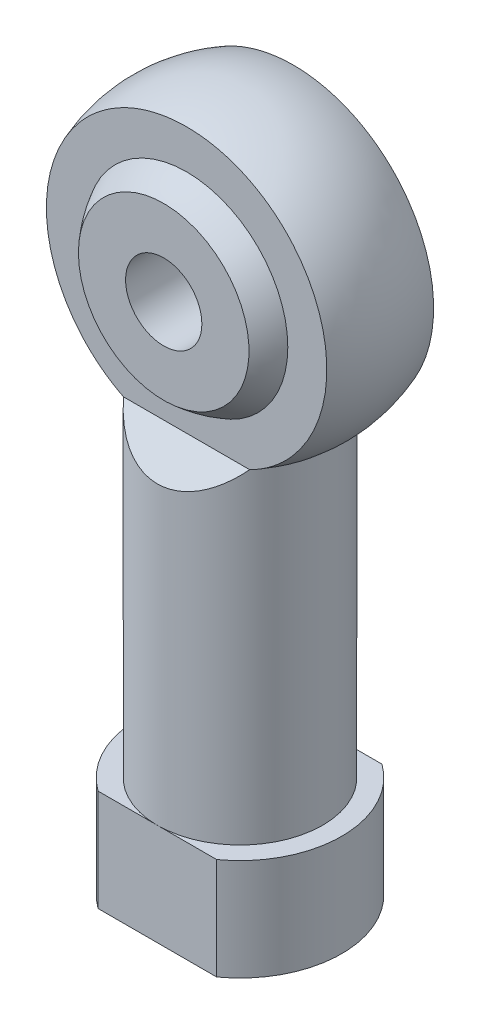
SolidWorks part; units mm, degrees
ref_plane "Alzado" through (0, 0, 0) normal (0, 0, 1) x (1, 0, 0)
ref_plane "Planta" through (0, 0, 0) normal (0, 1, 0) x (1, 0, 0)
ref_plane "Vista lateral" through (0, 0, 0) normal (1, 0, 0) x (0, 0, -1)
sketch "Croquis1" plane through (0, 0, 0) normal (0, 0, 1) x (1, 0, 0)
  line L0 (0, 0) -> (0, 17.2)
  line L1 (0, 0) -> (4, 0)
  line L2 (4, 0) -> (4, 4)
  line L3 (4, 4) -> (3.25, 4)
  line L4 (3.25, 4) -> (3.25, 16.7758)
  line L5 (0, 26.2) -> (0, 27.6)
  arc A0 (3.25, 16.7758) -> (0, 27.6) centre (0, 21.7) ccw
  arc A1 (0, 17.2) -> (0, 26.2) centre (0, 21.7) ccw
  dimension "D2" = 11.8
  dimension "D6" = 9
  dimension "D1" = 27.6
  dimension "D3" = 3.25
  dimension "D4" = 4
  dimension "D5" = 4
revolve "Revolución1" add sketch "Croquis1" angle 360 about L0
sketch "Croquis2" plane through (0, 0, 0) normal (1, 0, 0) x (0, 0, -1)
  line L0 (-3.25, 4) -> (-3.25, 0)
  line L5 (4, 4) -> (-4, 4) construction
  line L6 (-3.25, 16.7758) -> (-3.25, 4) construction
  line L7 (-4, 0) -> (4, 0) construction
  line L8 (-3.25, 4) -> (-4, 4)
  line L9 (-4, 4) -> (-4, 0)
  line L10 (-4, 0) -> (-3.25, 0)
  line L11 (0, -1000) -> (0, 49000) construction
  line L12 (3.25, 16.7758) -> (-3.25, 16.7758) construction
  line L13 (-2.1, 16.7758) -> (-5.9, 16.7758)
  line L14 (-2.1, 16.7758) -> (-2.1, 27.6)
  line L15 (-2.1, 27.6) -> (-5.9, 27.6)
  line L16 (-5.9, 16.7758) -> (-5.9, 27.6)
  line L17 (4, 0) -> (3.25, 0)
  line L18 (4, 4) -> (4, 0)
  line L19 (3.25, 4) -> (4, 4)
  line L20 (3.25, 4) -> (3.25, 0)
  line L21 (2.1, 27.6) -> (5.9, 27.6)
  line L22 (5.9, 16.7758) -> (5.9, 27.6)
  line L23 (2.1, 16.7758) -> (5.9, 16.7758)
  line L24 (2.1, 16.7758) -> (2.1, 27.6)
  line L25 (-2.1, 16.7758) -> (-3.25, 15.6258)
  line L26 (-3.25, 15.6258) -> (-3.25, 16.7758)
  line L27 (-3.25, 16.7758) -> (-3.25, 4) construction
  line L29 (2.1, 16.7758) -> (3.25, 15.6258)
  line L30 (3.25, 15.6258) -> (3.25, 16.7758)
  arc A0 (3.25, 16.7758) -> (-3.25, 16.7758) centre (0, 21.7) ccw construction
  dimension "D1" = 4.2
  dimension "D2" = 45
extrude "Cortar-Extruir1" cut sketch "Croquis2" against normal through all both and the other way through all contours L16 L13 L14 L15 | L24 L23 L22 L21 | L26 L25 L13 | L29 L30 L23 | L19 L20 L17 L18 | L9 L10 L0 L8
sketch "Croquis3" plane through (0, 0, 0) normal (0, 0, 1) x (1, 0, 0)
  line L0 (0, 26.2) -> (0, 17.2)
  arc A0 (0, 26.2) -> (0, 17.2) centre (0, 21.7) ccw
  circle A1 centre (0, 21.7) radius 4.5 construction
  dimension "D1" = 9
revolve "Revolución2" add sketch "Croquis3" angle 360 about L0
sketch "Croquis4" plane through (0, 0, 0) normal (1, 0, 0) x (0, 0, -1)
  line L0 (0, -1000) -> (0, 49000) construction
  line L1 (-3, 18.3459) -> (-4.8775, 18.3459)
  line L2 (-3, 18.3459) -> (-3, 25.0892)
  line L3 (-3, 25.0892) -> (-4.8775, 25.0892)
  line L4 (-4.8775, 18.3459) -> (-4.8775, 25.0892)
  line L5 (3, 25.0892) -> (4.8775, 25.0892)
  line L6 (4.8775, 18.3459) -> (4.8775, 25.0892)
  line L7 (3, 18.3459) -> (4.8775, 18.3459)
  line L8 (3, 18.3459) -> (3, 25.0892)
  arc A0 (-2.1, 25.6799) -> (-2.1, 17.7201) centre (0, 21.7) ccw construction
  dimension "D1" = 6
extrude "Cortar-Extruir2" cut sketch "Croquis4" against normal through all both and the other way through all
sketch "Croquis5" plane through (0, 0, 0) normal (0, 0, 1) x (1, 0, 0)
  circle A0 centre (0, 21.7) radius 1.5
  circle A1 centre (0, 21.7) radius 3.3541 construction
  dimension "D1" = 3
extrude "Cortar-Extruir3" cut sketch "Croquis5" against normal through all both and the other way through all
hole_wizard "Taladro roscado M31" positions "Croquis6" profile "Croquis7" tap size "M3" standard "ISO"
sketch "Croquis6" plane through (0, 0, 0) normal (0, -1, 0) x (-1, 0, 0)
  point P0 (0, 0)
sketch "Croquis7" plane through (0, 0, 0) normal (1, 0, 0) x (0, 0, -1)
  line L0 (0, 0) -> (0, 14.7511)
  line L1 (0, 14.7511) -> (1.25, 14)
  line L2 (1.25, 14) -> (1.25, 0)
  line L5 (1.25, 0) -> (0, 0)
  line L10 (0, 14.7511) -> (-1.25, 14) construction
  line L11 (0, -6.35) -> (0, 107.95) construction
  dimension "Diámetro de perforador para roscar" = 2.5
  dimension "Profundidad de perforador para roscar" = 14
  dimension "Ángulo de perforador" = 118
cosmetic thread "Rosca de taladro1" parameters "D1"=6, "D2"=3
